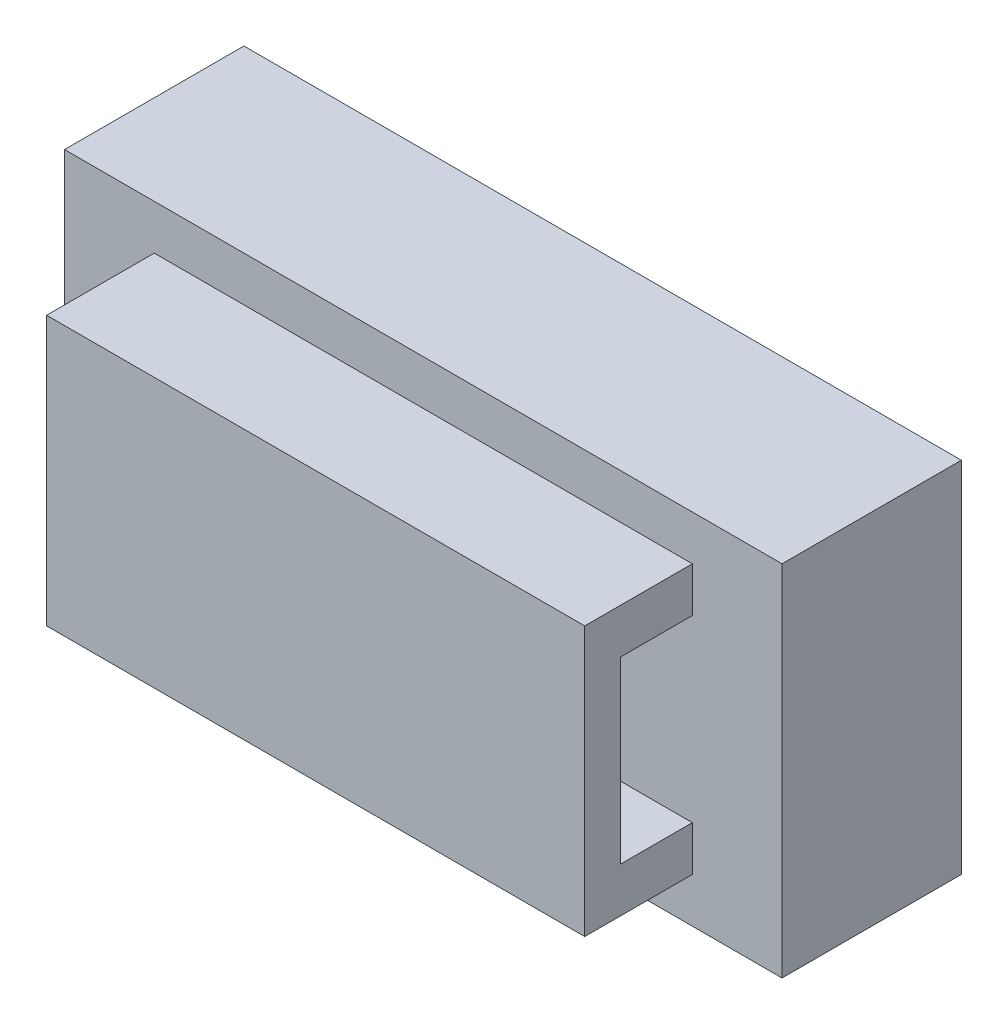
SolidWorks part; units mm, degrees
ref_plane "前视基准面" through (0, 0, 0) normal (0, 0, 1) x (1, 0, 0)
ref_plane "上视基准面" through (0, 0, 0) normal (0, 1, 0) x (1, 0, 0)
ref_plane "右视基准面" through (0, 0, 0) normal (1, 0, 0) x (0, 0, -1)
sketch "草图1" plane through (0, 0, 0) normal (0, 0, 1) x (1, 0, 0)
  line L1 (-20, 10) -> (20, 10)
  line L2 (-20, 10) -> (-20, -10)
  line L3 (-20, -10) -> (20, -10)
  line L4 (20, 10) -> (20, -10)
  line L5 (-20, 10) -> (20, -10) construction
  line L6 (-20, -10) -> (20, 10) construction
  point P0 (0, 0)
  dimension "D1" = 40
  dimension "D2" = 20
extrude "凸台-拉伸1" add sketch "草图1" along normal blind 10
sketch "草图2" plane through (0, 0, 10) normal (0, 0, 1) x (1, 0, 0)
  line L1 (-15, 7.5) -> (15, 7.5)
  line L2 (-15, 7.5) -> (-15, -7.5)
  line L3 (-15, -7.5) -> (15, -7.5)
  line L4 (15, 7.5) -> (15, -7.5)
  line L5 (-15, 7.5) -> (15, -7.5) construction
  line L6 (-15, -7.5) -> (15, 7.5) construction
  point P0 (0, 0)
  dimension "D1" = 15
  dimension "D2" = 30
extrude "凸台-拉伸2" add sketch "草图2" along normal blind 6
sketch "草图3" plane through (15, 0, 0) normal (1, 0, 0) x (0, 0, -1)
  line L0 (-10, -7.5) -> (-10, 7.5) construction
  line L1 (-10, -5) -> (-14, -5)
  line L2 (-10, -5) -> (-10, 5)
  line L3 (-10, 5) -> (-14, 5)
  line L4 (-14, -5) -> (-14, 5)
  dimension "D1" = 10
  dimension "D2" = 2.5
  dimension "D3" = 4
extrude "切除-拉伸1" cut sketch "草图3" against normal blind 40
